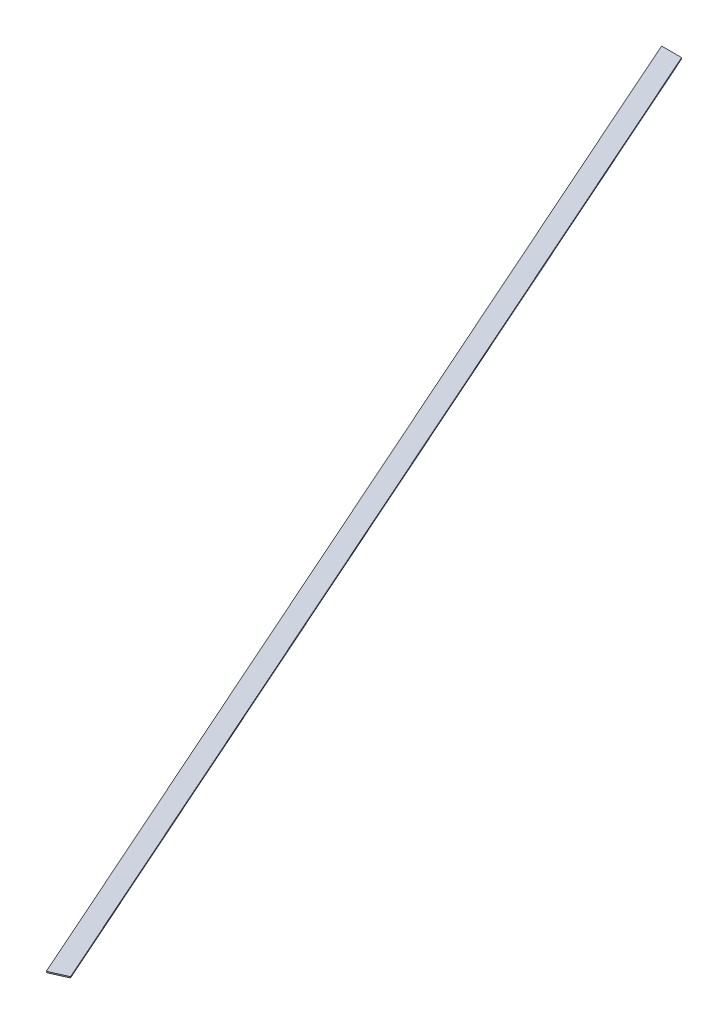
SolidWorks part; units mm, degrees
ref_plane "Front Plane" through (0, 0, 0) normal (0, 0, 1) x (1, 0, 0)
ref_plane "Top Plane" through (0, 0, 0) normal (0, 1, 0) x (1, 0, 0)
ref_plane "Right Plane" through (0, 0, 0) normal (1, 0, 0) x (0, 0, -1)
sketch "Sketch1" plane through (0, 0, 0) normal (0, 1, 0) x (1, 0, 0)
  line L0 (27.8038, 0) -> (-1804.2232, 4114.8)
  line L1 (-1804.2232, 4114.8) -> (-1859.8308, 4114.8)
  line L2 (-1859.8308, 4114.8) -> (-27.8038, 0)
  line L3 (-27.8038, 0) -> (27.8038, 0)
  dimension "D1" = 66
  dimension "D2" = 4114.8
  dimension "D3" = 50.8
extrude "Boss-Extrude1" add sketch "Sketch1" along normal blind 3.175
sketch "Sketch2" plane through (0, 3.175, 0) normal (0, 1, 0) x (1, 0, 0)
  line L0 (27.8038, 0) -> (-444.328, 1060.4253)
  line L5 (27.8038, 0) -> (-1804.2232, 4114.8) construction
  line L6 (-444.328, 1060.4253) -> (-490.7361, 1039.7631)
  line L7 (-1859.8308, 4114.8) -> (-27.8038, 0) construction
  line L8 (-490.7361, 1039.7631) -> (-27.8038, 0)
  line L9 (-27.8038, 0) -> (27.8038, 0)
  dimension "D1" = 1160.78
extrude "Cut-Extrude1" cut sketch "Sketch2" against normal through all
